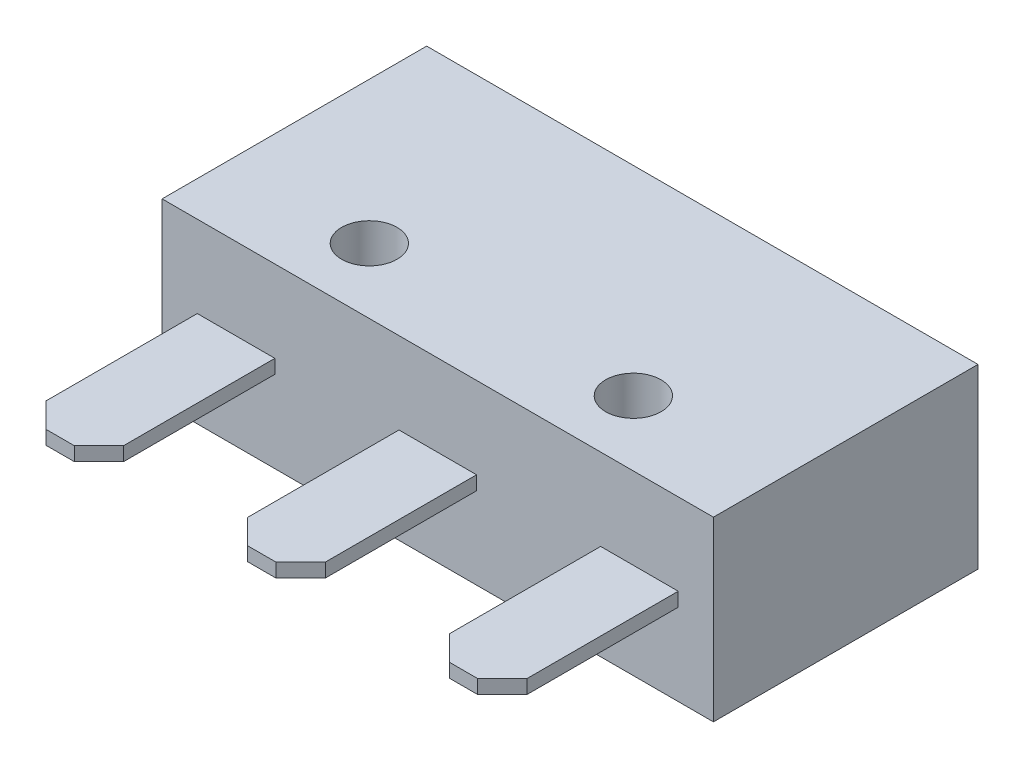
SolidWorks part; units mm, degrees
ref_plane "Front Plane" through (0, 0, 0) normal (0, 0, 1) x (1, 0, 0)
ref_plane "Top Plane" through (0, 0, 0) normal (0, 1, 0) x (1, 0, 0)
ref_plane "Right Plane" through (0, 0, 0) normal (1, 0, 0) x (0, 0, -1)
sketch "Sketch1" plane through (0, 0, 0) normal (0, 1, 0) x (1, 0, 0)
  line L1 (0, 0) -> (19.9, 0)
  line L2 (0, 0) -> (0, 9.55)
  line L3 (0, 9.55) -> (19.9, 9.55)
  line L4 (19.9, 0) -> (19.9, 9.55)
  circle A0 centre (5.13, 2.35) radius 1
  circle A1 centre (14.66, 2.35) radius 1
  dimension "D6" = 2
  dimension "D1" = 19.9
  dimension "D2" = 9.55
  dimension "D3" = 7.2
  dimension "D4" = 5.13
  dimension "D5" = 9.53
extrude "Boss-Extrude1" add sketch "Sketch1" along normal blind 6.4
sketch "Sketch2" plane through (0, 0, -9.55) normal (0, 0, -1) x (-1, 0, 0)
  line L0 (-13.66, 3.2) -> (-15.66, 3.2) construction
  line L1 (-13.66, 0) -> (-13.66, 6.4) construction
  line L2 (-15.66, 6.4) -> (-15.66, 0) construction
  line L3 (-14.66, 3.2) -> (-14.66, 6.4) construction
  line L4 (-19.9, 6.4) -> (0, 6.4) construction
  circle A0 centre (-7.1, 3.2) radius 1.5751
  dimension "D2" = 3.1501
  dimension "D1" = 7.56
extrude "Boss-Extrude2" add sketch "Sketch2" along normal blind 0.8636
sketch "Sketch3" plane through (0, 0, -10.4136) normal (0, 0, -1) x (-1, 0, 0)
  circle A0 centre (-7.1, 3.2) radius 0.7938
  circle A1 centre (-7.1, 3.2) radius 1.5751
  circle A2 centre (-7.1, 3.2) radius 1.5751 construction
  dimension "D1" = 1.5875
extrude "Cut-Extrude1" cut sketch "Sketch3" against normal blind 0.381
sketch "Sketch4" plane through (0, 0, 0) normal (0, 0, 1) x (1, 0, 0)
  line L0 (0, 3.2) -> (1.27, 3.2) construction
  line L1 (1.27, 3.45) -> (4.07, 3.45)
  line L2 (1.27, 3.45) -> (1.27, 2.95)
  line L3 (1.27, 2.95) -> (4.07, 2.95)
  line L4 (4.07, 3.45) -> (4.07, 2.95)
  line L5 (8.55, 3.45) -> (11.35, 3.45)
  line L6 (8.55, 3.45) -> (8.55, 2.95)
  line L7 (8.55, 2.95) -> (11.35, 2.95)
  line L8 (11.35, 3.45) -> (11.35, 2.95)
  line L9 (15.83, 3.45) -> (18.63, 3.45)
  line L10 (15.83, 3.45) -> (15.83, 2.95)
  line L11 (15.83, 2.95) -> (18.63, 2.95)
  line L12 (18.63, 3.45) -> (18.63, 2.95)
  line L13 (0, 6.4) -> (0, 0) construction
  line L14 (1.27, 3.2) -> (8.55, 3.2) construction
  line L15 (8.55, 3.2) -> (15.83, 3.2) construction
  line L16 (15.83, 3.2) -> (19.9, 3.2) construction
  line L17 (19.9, 6.4) -> (19.9, 0) construction
  line L18 (9.95, 3.45) -> (9.95, 6.4) construction
  line L19 (0, 6.4) -> (19.9, 6.4) construction
  dimension "D1" = 2.8
  dimension "D2" = 0.5
  dimension "D4" = 1.27
  dimension "D5" = 1.27
extrude "Boss-Extrude3" add sketch "Sketch4" along normal blind 6.35
chamfer "Chamfer1" distance 0.889 angle 45 6 edges at (15.83, 3.2, 6.35) (18.63, 3.2, 6.35) (11.35, 3.2, 6.35) (8.55, 3.2, 6.35) (4.07, 3.2, 6.35) (1.27, 3.2, 6.35)
